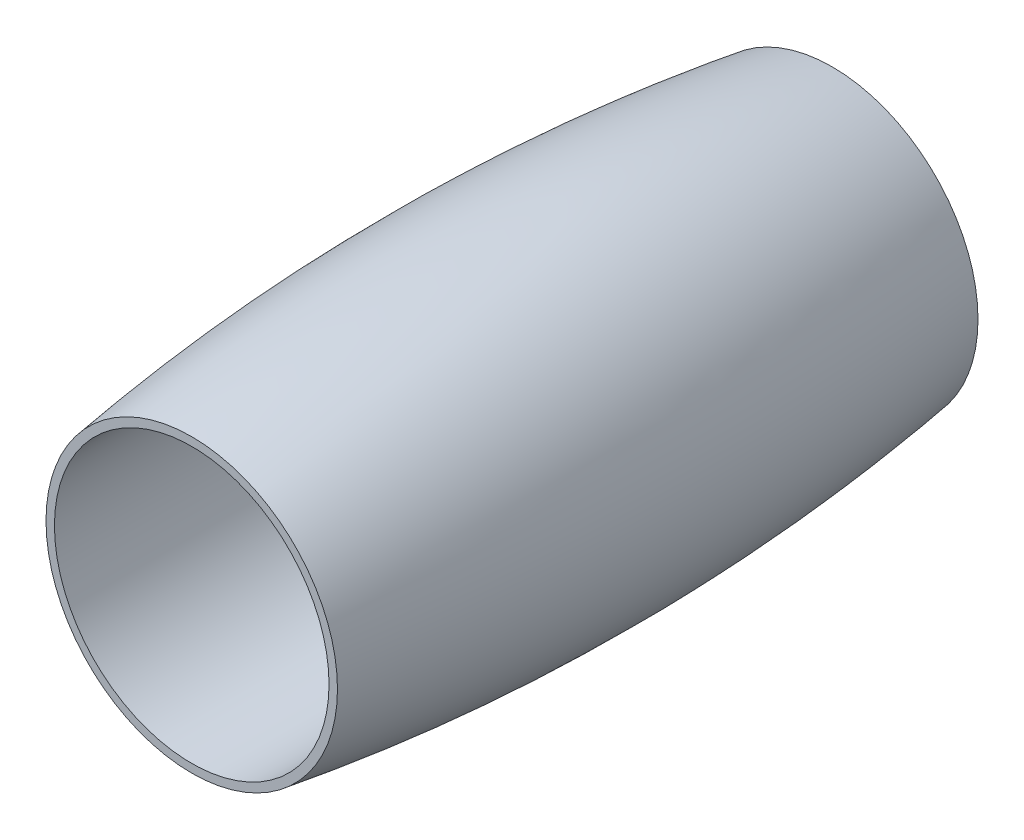
SolidWorks part; units mm, degrees
material "AISI 1020"
ref_plane "Спереди" through (0, 0, 0) normal (0, 0, 1) x (1, 0, 0)
ref_plane "Сверху" through (0, 0, 0) normal (0, 1, 0) x (1, 0, 0)
ref_plane "Справа" through (0, 0, 0) normal (1, 0, 0) x (0, 0, -1)
sketch "Эскиз1" plane through (0, 0, 0) normal (1, 0, 0) x (0, 0, -1)
  line L0 (-1000, 0) -> (49000, 0) construction
  line L1 (34.99, 15) -> (-34.99, 15) construction
  line L2 (34.99, 15) -> (-34.99, 15)
  line L3 (-34.99, 15.9217) -> (-34.99, 15)
  line L4 (34.99, 15.9217) -> (34.99, 15)
  ellipse E0 centre (0, -101.5) end of major axis (169.7056, -101.5) minor radius 120 (34.99, 15.9217) -> (0, 18.5) ccw construction
  ellipse E1 centre (0, -101.5) end of major axis (-169.7056, -101.5) minor radius 120 (0, 18.5) -> (-34.99, 15.9217) ccw construction
  ellipse E2 centre (0, -101.5) end of major axis (169.7056, -101.5) minor radius 120 (34.99, 15.9217) -> (0, 18.5) ccw
  ellipse E3 centre (0, -101.5) end of major axis (-169.7056, -101.5) minor radius 120 (0, 18.5) -> (-34.99, 15.9217) ccw
revolve "Повернуть1" add sketch "Эскиз1" angle 360 about L0
